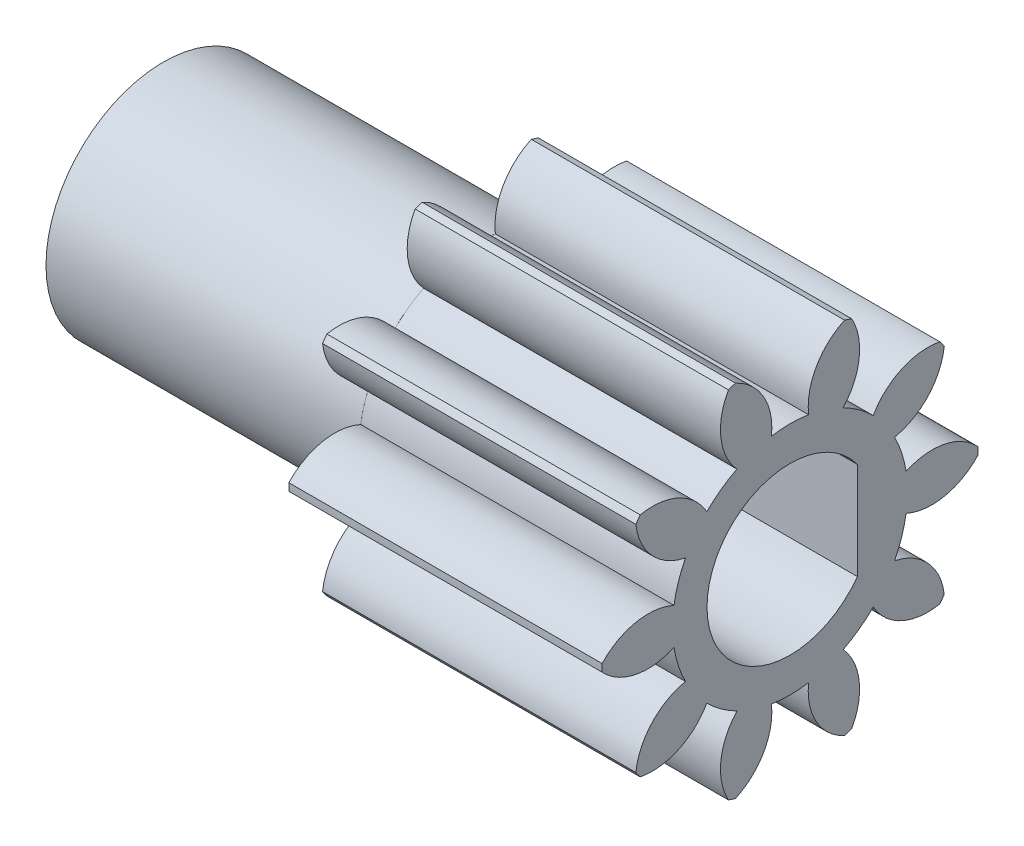
SolidWorks part; units mm, degrees
ref_plane "Plane1" through (0, 0, 0) normal (0, 0, 1) x (1, 0, 0)
ref_plane "Plane2" through (0, 0, 0) normal (0, 1, 0) x (1, 0, 0)
ref_plane "Plane3" through (0, 0, 0) normal (1, 0, 0) x (0, 0, -1)
sketch "HoldingSke" plane through (0, 0, 0) normal (0, 1, 0) x (1, 0, 0)
  line L0 (0, 0) -> (0.9848, -0.1736)
  line L1 (-15, 0) -> (100, 0) construction
  line L2 (0, 0) -> (-2.1039, 2.3779)
  line L3 (0, 0) -> (-11.863, 4.5341)
  line L4 (0, 0) -> (8.5048, 1.4996)
  line L5 (0, 0) -> (-46.8476, -17.4728)
  line L6 (0, 0) -> (-8.2896, -5.593)
  line L7 (-2.1039, 2.3779) -> (8.6586, 51.2059)
  line L8 (-76.2, 54.61) -> (-76.1, 54.61)
  line L9 (-71.009, 38.7566) -> (-53.1078, 45.2721)
  line L10 (-76.2, 71.12) -> (104.1128, 71.12)
  line L11 (0, 0) -> (-10, 0)
  line L12 (-76.2, 101.6) -> (-76.162, 101.6)
  line L13 (24.9733, 27.94) -> (52.9518, 28.4284)
  line L14 (24.9733, 27.94) -> (24.9743, 27.94)
  line L15 (24.9733, 27.94) -> (100.4006, 29.5858)
  line L16 (-63.627, -1) -> (-12.827, -1)
  circle A0 centre (0, 0) radius 0.4
  circle A1 centre (0, 0) radius 3.749
  circle A2 centre (0, 0) radius 37.5
  circle A3 centre (0, 0) radius 0.4
  dimension "MHD" = 7.498
  dimension "Hub_dia" = 75
  dimension "Bore" = 0.8
  dimension "MBD" = 0.8
  dimension "Num_teeth" = 10
  dimension "Pitch" = 1
  dimension "Overall_len" = 50
  dimension "Show_teeth" = 10
  dimension "Thickness" = 10
  dimension "OAL" = 50.0001
  dimension "T_dim" = 0.1
  dimension "Ap" = 20
  dimension "H" = 19.05
  dimension "Pitch_radius" = 180.3128
  dimension "Width" = 10
  dimension "Backlash" = 0.038
  dimension "Addendum_fac" = 1
  dimension "Dedendum_fac" = 1.25
  dimension "Clearance_fac" = 0.25
  dimension "Dedendum_add" = 0.001
  dimension "Module" = 1
sketch "BasProSke" plane through (0, 0, 0) normal (0, 1, 0) x (1, 0, 0)
  line L0 (-10, 0) -> (60, 0) construction
  line L1 (0, 0) -> (0, 6)
  line L2 (0, 0) -> (10, 0)
  line L3 (10, 0) -> (10, 6)
  line L4 (10, 6) -> (0, 6)
  dimension "Thickness" = 10
  dimension "Diameter" = 12
revolve "Base-Revolve" add sketch "BasProSke" angle 360 about L0
sketch "TooCutSke" plane through (0, 0, 0) normal (1, 0, 0) x (0, 0, -1)
  line L1 (0, 0) -> (0, 107) construction
  line L2 (0, 0) -> (-0.8485, 4.9275) construction
  line L3 (0, 0) -> (-3.0584, 9.4126) construction
  line L4 (-0.8485, 4.9275) -> (-1.5292, 4.7063) construction
  arc A0 (0.5928, 3.7018) -> (-0.5928, 3.7018) centre (0, 0) ccw
  arc A1 (1.7758, 5.7578) -> (-1.7758, 5.7578) centre (0, 0) ccw
  circle A2 centre (0, 0) radius 5 construction
  circle A3 centre (0, 0) radius 4.6985 construction
  arc A4 (-0.5928, 3.7018) -> (-1.7758, 5.7578) centre (-2.5801, 3.9267) ccw
  arc A5 (1.7758, 5.7578) -> (0.5928, 3.7018) centre (2.5801, 3.9267) ccw
  dimension "Root_dia" = 7.498
  dimension "Overcut_dia" = 12.0508
  dimension "Pitch_dia" = 10
  dimension "Base_dia" = 9.3969
  dimension "Flank_rad" = 2
  dimension "Half_ang" = 18
  dimension "Half_CT" = 0.7157
extrude "ToothCut" cut sketch "TooCutSke" along normal through all
fillet "Breaks" [suppressed] radius 0.02
fillet "RootFillets" [suppressed] radius 0.251
pattern_circular "TeethCuts" count 10 every 36 about axis through (-10, 0, 0) along (1, 0, 0) of "ToothCut", "RootFillets", "Breaks"
sketch "HubNeaOneSke" plane through (0, 0, 0) normal (-1, 0, 0) x (0, 0, 1)
  circle A0 centre (0, 0) radius 3.749
  dimension "Diameter" = 7.498
extrude "HubNearOne" [suppressed] add sketch "HubNeaOneSke" along normal blind 40.0001
sketch "HubNeaBotSke" plane through (0, 0, 0) normal (-1, 0, 0) x (0, 0, 1)
  circle A0 centre (0, 0) radius 3.749
  dimension "Diameter" = 7.498
extrude "HubNearBoth" [suppressed] add sketch "HubNeaBotSke" along normal blind 20
ref_plane "FarPln" through (10, 0, 0) normal (1, 0, 0) x (0, 0, -1)
sketch "HubFarSke" plane through (10, 0, 0) normal (1, 0, 0) x (0, 0, -1)
  circle A0 centre (0, 0) radius 3.749
  dimension "Diameter" = 7.498
extrude "HubFar" [suppressed] add sketch "HubFarSke" along normal blind 20
sketch "BorSke" plane through (0, 0, 0) normal (1, 0, 0) x (0, 0, -1)
  circle A0 centre (0, 0) radius 0.4
  dimension "Diameter" = 0.8
extrude "Bore" cut sketch "BorSke" along normal mid plane 100.0001
sketch "KeySke" plane through (0, 0, 0) normal (1, 0, 0) x (0, 0, -1)
  line L0 (-0.05, 0) -> (-0.05, 0.5)
  line L1 (-0.05, 0.5) -> (0.05, 0.5)
  line L2 (0.05, 0.5) -> (0.05, 0)
  line L3 (0, 0) -> (0, 34) construction
  line L4 (-0.05, 0) -> (0.05, 0)
  dimension "Offset" = 0.5
  dimension "Width" = 0.1
extrude "Keyway" [suppressed] cut sketch "KeySke" along normal mid plane 100.0001
pattern_circular "Keyway2" [suppressed] count 2 every 90 about axis through (-10, 0, 0) along (1, 0, 0)
sketch "Croquis1" plane through (0, 0, 0) normal (-1, 0, 0) x (0, 0, 1)
  circle A0 centre (0, 0) radius 3.75
  dimension "D1" = 7.5
extrude "Saliente-Extruir1" add sketch "Croquis1" along normal blind 10
hole_wizard "Taladro de margen para M51" positions "Croquis3" profile "Croquis4" hole size "M5" standard "ISO" end condition through all
sketch "Croquis3" plane through (-10, 0, 0) normal (-1, 0, 0) x (0, 0, 1)
  point P0 (0, 0)
sketch "Croquis4" plane through (-10, 0, 0) normal (0, 1, 0) x (0, 0, 1)
  line L0 (0, 0) -> (0, 20)
  line L1 (0, 20) -> (2.65, 20)
  line L2 (2.65, 20) -> (2.65, 0)
  line L5 (2.65, 0) -> (0, 0)
  line L11 (0, -6.35) -> (0, 107.95) construction
  dimension "Diámetro de taladro hasta el siguiente" = 5.3
  dimension "Profundidad de taladro hasta el siguiente" = 20
sketch "Croquis5" plane through (10, 0, 0) normal (1, 0, 0) x (0, 0, -1)
  line L0 (-2.3506, 0) -> (2.1494, 0) construction
  line L1 (2.1494, 0) -> (2.1494, 1.55)
  line L2 (2.1494, 0) -> (2.1494, -1.55)
  circle A0 centre (0, 0) radius 2.65 construction
  arc A1 (2.1494, -1.55) -> (2.1494, 1.55) centre (0, 0) ccw
  dimension "D1" = 4.5
  dimension "D2" = 1.55
extrude "Saliente-Extruir2" add sketch "Croquis5" against normal blind 10
equation "' \"Module@HoldingSke\" = 6.35"
equation "' \"Num_teeth@HoldingSke\" = 12"
equation "' \"Ap@HoldingSke\" =  20"
equation "' \"Ap@HoldingSke\" = 20"
equation "' \"Width@HoldingSke\" = 0.5 * 25.4"
equation "' \"Hub_dia@HoldingSke\"= 1 * 25.4"
equation "' \"Hub_dia@HoldingSke\" = 1 * 25.4"
equation "' \"Overall_len@HoldingSke\" = 1.0 * 25.4"
equation "' \"Bore@HoldingSke\" = 0.75 * 25.4"
equation "' \"T_dim@HoldingSke\" = 0.1 * 25.4"
equation "' \"Width@KeySke\" = 0.25 * 25.4"
equation "' \"Show_teeth@HoldingSke\" = 13"
equation "' \"Backlash@HoldingSke\" = 0.009 * 25.4"
equation "' \"Addendum_fac@HoldingSke\" = 1.0"
equation "' \"Dedendum_fac@HoldingSke\" = 1.25"
equation "' \"Dedendum_add@HoldingSke\" = 0.00005 * 25.4"
equation "' \"Clearance_fac@HoldingSke\" = 0.25"
equation "\"Pitch@HoldingSke\" = 1 / \"Module@HoldingSke\""
equation "\"Overcut_dia@TooCutSke\" = (\"Num_teeth@HoldingSke\" + 2 * \"Addendum_fac@HoldingSke\") / \"Pitch@HoldingSke\" + 0.002 * 25.4"
equation "\"Pitch_dia@TooCutSke\" = \"Num_teeth@HoldingSke\" / \"Pitch@HoldingSke\""
equation "\"Base_dia@TooCutSke\" = \"Num_teeth@HoldingSke\" / \"Pitch@HoldingSke\" * cos((\"Ap@HoldingSke\"  * 3.14159265 / 180))"
equation "\"Root_dia@TooCutSke\" = (\"Num_teeth@HoldingSke\" + 2) / \"Pitch@HoldingSke\" - 2 * (\"Addendum_fac@HoldingSke\" + \"Dedendum_fac@HoldingSke\") / \"Pitch@HoldingSke\" - \"Dedendum_add@HoldingSke\" * 2"
equation "\"Half_ang@TooCutSke\" = 180 / \"Num_teeth@HoldingSke\""
equation "\"Half_CT@TooCutSke\" = \"Num_teeth@HoldingSke\" / \"Pitch@HoldingSke\" * sin((3.14159265 / 2 / \"Num_teeth@HoldingSke\")) / 2 - 7 * \"Backlash@HoldingSke\" / 4"
equation "\"Flank_rad@TooCutSke\" = \"Num_teeth@HoldingSke\" / \"Pitch@HoldingSke\" / 5"
equation "\"Radius@RootFillets\" = \"Clearance_fac@HoldingSke\" / \"Pitch@HoldingSke\" + \"Dedendum_add@HoldingSke\""
equation "\"Break_rad@Breaks\" = 0.02 / \"Pitch@HoldingSke\""
equation "\"Thickness@HoldingSke\" = \"Width@HoldingSke\""
equation "\"OAL@HoldingSke\" = \"Thickness@HoldingSke\""
equation "\"MHD@HoldingSke\" = (\"Num_teeth@HoldingSke\" + 2) / \"Pitch@HoldingSke\" - 2 * (\"Addendum_fac@HoldingSke\" + \"Dedendum_fac@HoldingSke\")  / \"Pitch@HoldingSke\" - \"Dedendum_add@HoldingSke\" * 2"
equation "\"MBD@HoldingSke\" = (\"Num_teeth@HoldingSke\" + 2) / \"Pitch@HoldingSke\" - 2 * (\"Addendum_fac@HoldingSke\" + \"Dedendum_fac@HoldingSke\")  / \"Pitch@HoldingSke\" - \"Dedendum_add@HoldingSke\" * 2 - 0.002 * 25.4"
equation "\"MHD@HoldingSke\" = ((sgn( \"MHD@HoldingSke\" - \"Hub_dia@HoldingSke\" )-1)*( \"MHD@HoldingSke\" - \"Hub_dia@HoldingSke\" ))/-2+ \"Hub_dia@HoldingSke\""
equation "\"MBD@HoldingSke\" = ((sgn( \"MBD@HoldingSke\" - \"Bore@HoldingSke\" )-1)*( \"MBD@HoldingSke\" - \"Bore@HoldingSke\" ))/-2+ \"Bore@HoldingSke\""
equation "\"OAL@HoldingSke\" = ((sgn( \"OAL@HoldingSke\" - \"Overall_len@HoldingSke\" )+1)*( \"OAL@HoldingSke\" - \"Overall_len@HoldingSke\" ))/2 + \"Overall_len@HoldingSke\" + 0.000002 * 25.4"
equation "\"Num_teeth@TeethCuts\" = int( \"Show_teeth@HoldingSke\" ) + 1"
equation "\"Num_teeth@TeethCuts\" = ((sgn( \"Num_teeth@TeethCuts\" - \"Num_teeth@HoldingSke\" )-1)*( \"Num_teeth@TeethCuts\" - \"Num_teeth@HoldingSke\" ))/-2+ \"Num_teeth@HoldingSke\""
equation "\"Num_teeth@TeethCuts\" = ((sgn( \"Num_teeth@TeethCuts\" - 2.0)+1)*( \"Num_teeth@TeethCuts\" - 2.0))/2 +2.0"
equation "\"Angle@TeethCuts\" = 360.0 / \"Num_teeth@HoldingSke\""
equation "\"Diameter@BasProSke\" = (\"Num_teeth@HoldingSke\" + 2 * \"Addendum_fac@HoldingSke\") / \"Pitch@HoldingSke\""
equation "\"Thickness@BasProSke\"  = \"Thickness@HoldingSke\""
equation "' \"Fillet_rad@BasProSke\" =  \"Thickness@HoldingSke\" * 0.05"
equation "' \"Fillet_rad@BasProSke\" = \"Thickness@HoldingSke\" * 0.05"
equation "\"MHD@HoldingSke\" = ((sgn( \"MHD@HoldingSke\" - \"Root_dia@TooCutSke\" )-1)*( \"MHD@HoldingSke\" - \"Root_dia@TooCutSke\" ))/-2+ \"Root_dia@TooCutSke\""
equation "\"Diameter@HubNeaOneSke\" = \"MHD@HoldingSke\""
equation "\"Length@HubNearOne\" = \"OAL@HoldingSke\" - \"Thickness@BasProSke\""
equation "\"Diameter@HubNeaBotSke\" = \"MHD@HoldingSke\""
equation "\"Length@HubNearBoth\" = ( \"OAL@HoldingSke\" - \"Thickness@BasProSke\" ) / 2.0"
equation "\"Thickness@FarPln\" = \"Thickness@BasProSke\""
equation "\"Diameter@HubFarSke\" = \"MHD@HoldingSke\""
equation "\"Length@HubFar\" = ( \"OAL@HoldingSke\" - \"Thickness@BasProSke\" ) / 2.0"
equation "\"Diameter@BorSke\" = \"MBD@HoldingSke\""
equation "\"D1@Bore\" = \"OAL@HoldingSke\" * 2.0"
equation "\"D1@Keyway\" = \"OAL@HoldingSke\" * 2.0"
equation "\"Offset@KeySke\" = \"T_dim@HoldingSke\" + \"MBD@HoldingSke\" / 2.0"
